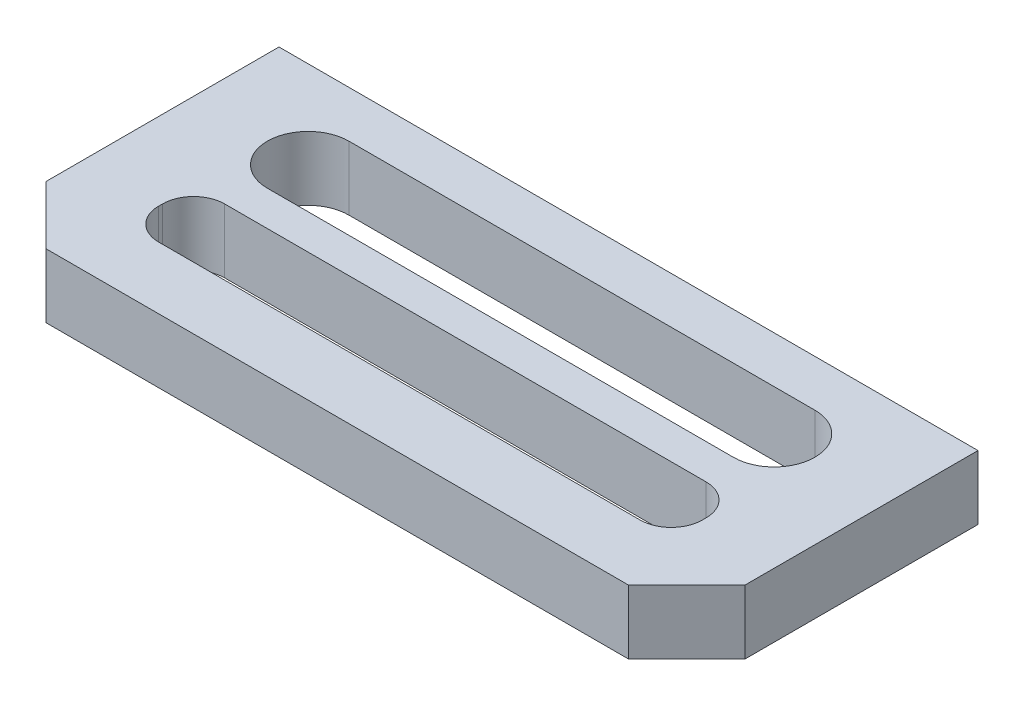
SolidWorks part; units mm, degrees
material "PVC hart"
ref_plane "Ebene vorne" through (0, 0, 0) normal (0, 0, 1) x (1, 0, 0)
ref_plane "Ebene oben" through (0, 0, 0) normal (0, 1, 0) x (1, 0, 0)
ref_plane "Ebene rechts" through (0, 0, 0) normal (1, 0, 0) x (0, 0, -1)
sketch "Skizze1" plane through (0, 0, 0) normal (0, 1, 0) x (1, 0, 0)
  line L0 (-9, 0) -> (9, 0) construction
  line L1 (-9, 3.75) -> (9, 3.75)
  line L2 (-9, 3.75) -> (-9, -3.75)
  line L3 (-9, -3.75) -> (9, -3.75)
  line L4 (9, 3.75) -> (9, -3.75)
  line L6 (-7, -0.45) -> (7, -0.45)
  line L7 (-7, -0.45) -> (-7, -2.15)
  line L8 (-7, -2.15) -> (7, -2.15)
  line L9 (7, -0.45) -> (7, -2.15)
  line L10 (-6, 1.5) -> (6, 1.5) construction
  line L11 (-6, 2.55) -> (6, 2.55)
  line L12 (-6, 0.45) -> (6, 0.45)
  line L13 (0, 0) -> (0, -0.45) construction
  line L14 (0, 1.5) -> (0, 0) construction
  arc A0 (-6, 2.55) -> (-6, 0.45) centre (-6, 1.5) ccw
  arc A1 (6, 0.45) -> (6, 2.55) centre (6, 1.5) ccw
  point P14 (0, 1.5)
  dimension "D5" = 4.2
  dimension "D6" = 12
  dimension "D7" = 1.05
  dimension "D8" = 2.25
  dimension "D1" = 18
  dimension "D2" = 14
  dimension "D3" = 1.7
  dimension "D4" = 1.6
extrude "Aufsatz-Linear austragen1" add sketch "Skizze1" against normal mid plane 1.65
fillet "Verrundung1" radius 0.8 4 edges at (7, 0, 0.45) (7, 0, 2.15) (-7, 0, 2.15) (-7, 0, 0.45)
chamfer "Fase1" distance 1.5 angle 45 2 edges at (-9, 0, 3.75) (9, 0, 3.75)
